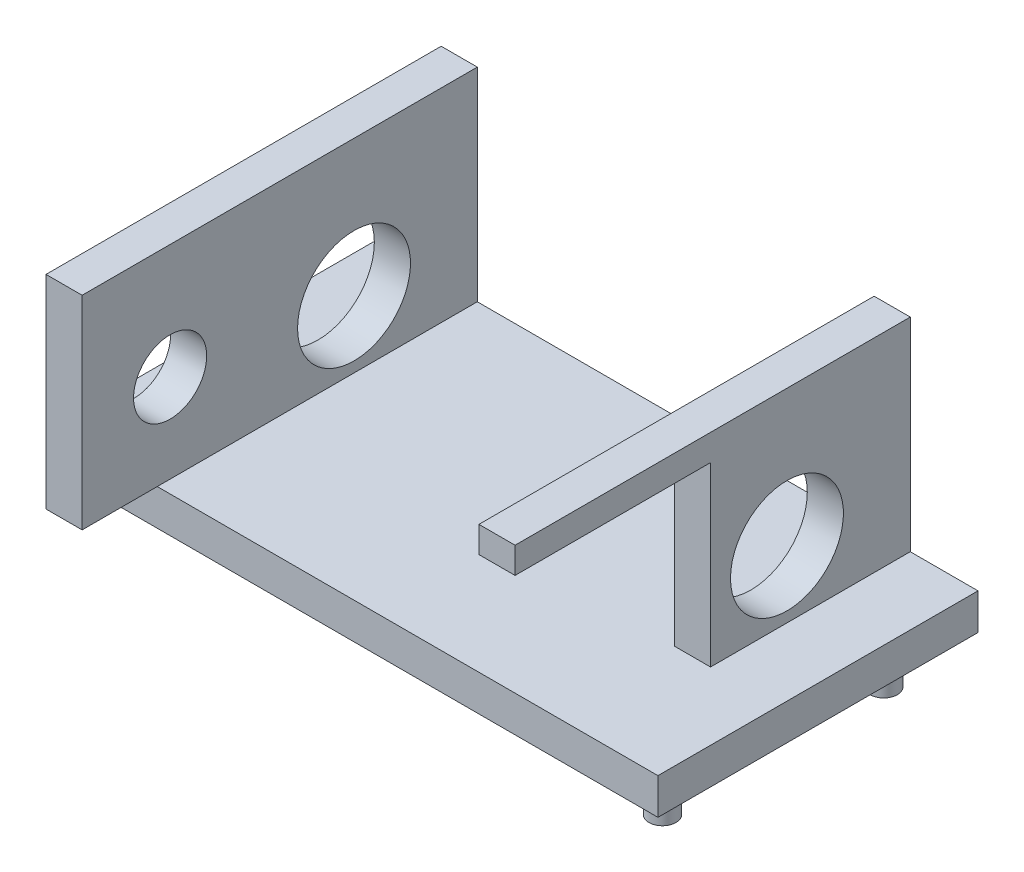
SolidWorks part; units mm, degrees
ref_plane "Front Plane" through (0, 0, 0) normal (0, 0, 1) x (1, 0, 0)
ref_plane "Top Plane" through (0, 0, 0) normal (0, 1, 0) x (1, 0, 0)
ref_plane "Right Plane" through (0, 0, 0) normal (1, 0, 0) x (0, 0, -1)
sketch "Sketch1" plane through (0, 0, 0) normal (0, 1, 0) x (1, 0, 0)
  line L1 (-17, 9) -> (17, 9)
  line L2 (-17, 9) -> (-17, -9)
  line L3 (-17, -9) -> (17, -9)
  line L4 (17, 9) -> (17, -9)
  line L5 (-17, 9) -> (17, -9) construction
  line L6 (-17, -9) -> (17, 9) construction
  point P0 (0, 0)
  dimension "D1" = 34
  dimension "D2" = 18
extrude "Boss-Extrude1" add sketch "Sketch1" along normal blind 2.032
sketch "Sketch2" plane through (0, 0, 0) normal (0, -1, 0) x (-1, 0, 0)
  line L0 (-15.476, -9) -> (-15.476, 9) construction
  line L1 (17, -9) -> (-17, -9) construction
  line L2 (-17, 9) -> (17, 9) construction
  line L3 (15.476, -9) -> (15.476, 9) construction
  line L4 (-17, -9) -> (-17, 9) construction
  line L5 (17, 9) -> (17, -9) construction
  line L6 (-17, -6.46) -> (17, -6.46) construction
  circle A0 centre (-15.476, 5.224) radius 0.762
  circle A1 centre (-15.476, -7.222) radius 0.762
  circle A2 centre (15.476, -7.222) radius 0.762
  circle A3 centre (15.476, 6.494) radius 0.762
  dimension "D3" = 1.524
  dimension "D4" = 2.54
  dimension "D5" = 13.716
  dimension "D1" = 1.524
  dimension "D2" = 1.524
  dimension "D6" = 12.446
extrude "Boss-Extrude2" add sketch "Sketch2" along normal blind 1.524
sketch "Sketch3" plane through (-17, 0, 0) normal (-1, 0, 0) x (0, 0, 1)
  line L0 (-9, 2.032) -> (9, 2.032) construction
  line L1 (-9, 0) -> (9, 0) construction
  line L4 (-9, 2.032) -> (-9, 0) construction
  circle A0 centre (-2.0658, 5.7912) radius 3.175
  circle A1 centre (8.2766, 7.0104) radius 2.0574
  dimension "D3" = 5.7912
  dimension "D1" = 4.1148
  dimension "D2" = 6.35
  dimension "D6" = 6.9342
  dimension "D4" = 10.414
  dimension "D5" = 4.9784
sketch "Sketch4" plane through (0, 2.032, 0) normal (0, 1, 0) x (1, 0, 0)
  line L0 (17, 9) -> (-17, 9) construction
  line L1 (-13.19, 9) -> (-11.158, 9)
  line L2 (-13.19, 9) -> (-13.19, -13.225)
  line L3 (-13.19, -13.225) -> (-11.158, -13.225)
  line L4 (-11.158, 9) -> (-11.158, -13.225)
  line L5 (-17, 9) -> (-17, -9) construction
  line L6 (13.19, 9) -> (11.158, 9)
  line L7 (13.19, 9) -> (13.19, -13.225)
  line L8 (13.19, -13.225) -> (11.158, -13.225)
  line L9 (11.158, 9) -> (11.158, -13.225)
  line L10 (17, -9) -> (17, 9) construction
  dimension "D1" = 2.032
  dimension "D2" = 22.225
  dimension "D3" = 3.81
  dimension "D4" = 3.81
extrude "Boss-Extrude3" add sketch "Sketch4" along normal blind 11.43
extrude "Cut-Extrude1" cut sketch "Sketch3" against normal through all both and the other way through all
sketch "Sketch5" plane through (13.19, 0, 0) normal (1, 0, 0) x (0, 0, -1)
  line L2 (-14.3218, 11.9888) -> (-2.2314, 11.9888)
  line L3 (-14.3218, 11.9888) -> (-14.3218, 2.032)
  line L4 (-14.3218, 2.032) -> (-2.2314, 2.032)
  line L5 (-2.2314, 11.9888) -> (-2.2314, 2.032)
  line L6 (-14.3218, 11.9888) -> (-2.2314, 2.032) construction
  line L7 (-14.3218, 2.032) -> (-2.2314, 11.9888) construction
  point P0 (-8.2766, 7.0104)
  dimension "D1" = 9.9568
  dimension "D2" = 12.0904
extrude "Cut-Extrude2" cut sketch "Sketch5" against normal up to surface (2.032 mm away) up to face at (11.158, 5.7912, -5.2408)
